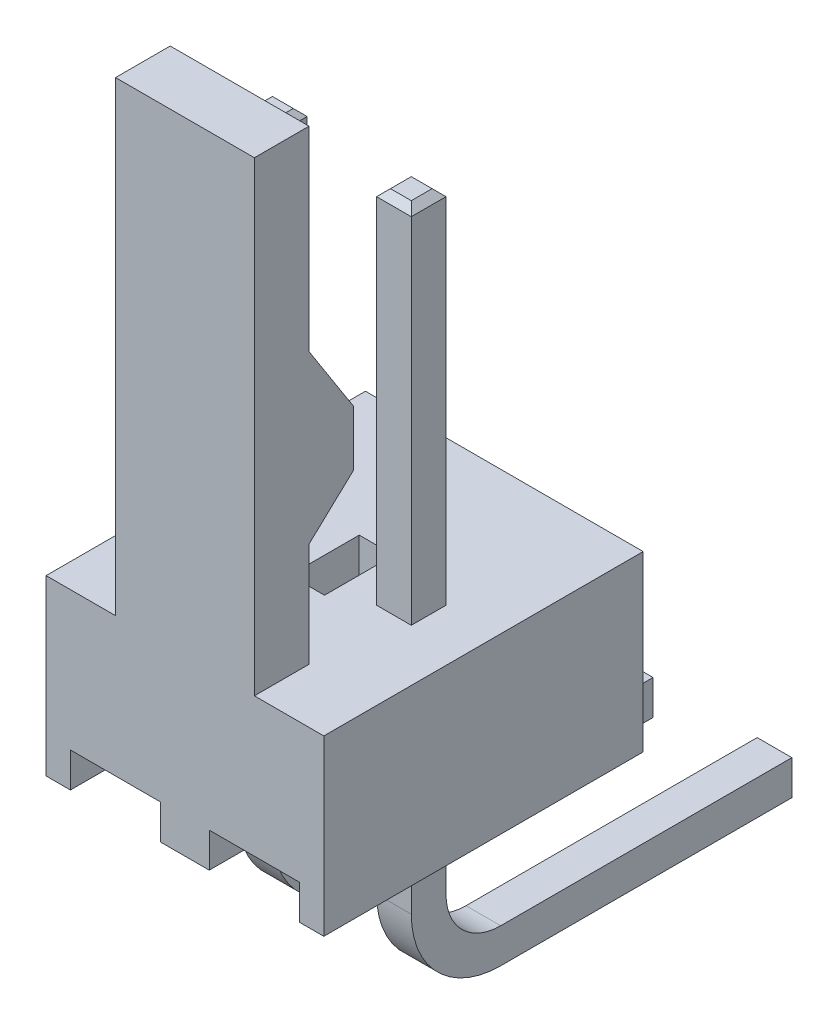
SolidWorks part; units mm, degrees
ref_plane "Płaszczyzna przednia" through (0, 0, 0) normal (0, 0, 1) x (1, 0, 0)
ref_plane "Płaszczyzna górna" through (0, 0, 0) normal (0, 1, 0) x (1, 0, 0)
ref_plane "Płaszczyzna prawa" through (0, 0, 0) normal (1, 0, 0) x (0, 0, -1)
ref_plane "Plane15" through (1.5875, 0, 0) normal (1, 0, 0) x (0, 0, -1)
sketch "Sketch68" plane through (1.5875, 0, 0) normal (1, 0, 0) x (0, 0, -1)
  line L0 (3.8, -0.3175) -> (3.8, 3.355)
  line L1 (3.8, 3.355) -> (-3.2893, 3.355)
  line L2 (-3.2893, 3.355) -> (-3.2893, -0.3175)
  line L3 (-3.2893, -0.3175) -> (3.8, -0.3175)
extrude "Boss-Extrude17" add sketch "Sketch68" against normal blind 0.635 separate body
sketch "Sketch69" plane through (0.9525, 0, 0) normal (-1, 0, 0) x (0, 0, 1)
  line L0 (-3.8, 0.3175) -> (2.6543, 0.3175)
  line L1 (2.6543, 0.3175) -> (2.6543, 3.355)
  line L2 (2.6543, 3.355) -> (-3.8, 3.355)
  line L3 (-3.8, 3.355) -> (-3.8, 0.3175)
extrude "Cut-Extrude12" cut sketch "Sketch69" against normal through all
chamfer "Chamfer15" distance 0.127 angle 45 4 edges at (0.9525, 0, -3.8) (1.27, -0.3175, -3.8) (1.27, 0.3175, -3.8) (1.5875, 0, -3.8)
fillet "Fillet17" radius 1 1 edges at (1.27, 0.3175, 2.6543)
fillet "Fillet18" radius 1.635 1 edges at (1.27, -0.3175, 3.2893)
ref_plane "Plane16" through (-0.9525, 0, 0) normal (1, 0, 0) x (0, 0, -1)
sketch "Sketch74" plane through (-0.9525, 0, 0) normal (1, 0, 0) x (0, 0, -1)
  line L0 (3.8, -0.3175) -> (3.8, 3.355)
  line L1 (3.8, 3.355) -> (-3.2893, 3.355)
  line L2 (-3.2893, 3.355) -> (-3.2893, -0.3175)
  line L3 (-3.2893, -0.3175) -> (3.8, -0.3175)
extrude "Boss-Extrude18" add sketch "Sketch74" against normal blind 0.635 separate body
sketch "Sketch75" plane through (-1.5875, 0, 0) normal (-1, 0, 0) x (0, 0, 1)
  line L0 (-3.8, 0.3175) -> (2.6543, 0.3175)
  line L1 (2.6543, 0.3175) -> (2.6543, 3.355)
  line L2 (2.6543, 3.355) -> (-3.8, 3.355)
  line L3 (-3.8, 3.355) -> (-3.8, 0.3175)
extrude "Cut-Extrude13" cut sketch "Sketch75" against normal through all
chamfer "Chamfer16" distance 0.127 angle 45 4 edges at (-1.5875, 0, -3.8) (-1.27, -0.3175, -3.8) (-1.27, 0.3175, -3.8) (-0.9525, 0, -3.8)
fillet "Fillet19" radius 1 1 edges at (-1.27, 0.3175, 2.6543)
fillet "Fillet20" radius 1.635 1 edges at (-1.27, -0.3175, 3.2893)
ref_plane "Plane17" through (0, 0, 2.6543) normal (0, 0, -1) x (-1, 0, 0)
sketch "Sketch81" plane through (0, 0, 2.6543) normal (0, 0, -1) x (-1, 0, 0)
  line L0 (-0.9525, 5.895) -> (-0.9525, 12.368)
  line L1 (-0.9525, 12.368) -> (-0.9525, 12.495)
  line L2 (-0.9525, 12.495) -> (-1.5875, 12.495)
  line L3 (-1.5875, 12.495) -> (-1.5875, 12.368)
  line L4 (-1.5875, 12.368) -> (-1.5875, 5.895)
  line L5 (-1.5875, 5.895) -> (-0.9525, 5.895)
extrude "Boss-Extrude19" add sketch "Sketch81" against normal blind 0.635 separate body
chamfer "Chamfer17" distance 0.127 angle 45 4 edges at (1.27, 12.495, 3.2893) (0.9525, 12.495, 2.9718) (1.5875, 12.495, 2.9718) (1.27, 12.495, 2.6543)
sketch "Sketch88" plane through (0, 0, 2.6543) normal (0, 0, -1) x (-1, 0, 0)
  line L0 (1.5875, 5.895) -> (1.5875, 12.368)
  line L1 (1.5875, 12.368) -> (1.5875, 12.495)
  line L2 (1.5875, 12.495) -> (0.9525, 12.495)
  line L3 (0.9525, 12.495) -> (0.9525, 12.368)
  line L4 (0.9525, 12.368) -> (0.9525, 5.895)
  line L5 (0.9525, 5.895) -> (1.5875, 5.895)
extrude "Boss-Extrude20" add sketch "Sketch88" against normal blind 0.635 separate body
chamfer "Chamfer18" distance 0.127 angle 45 4 edges at (-1.27, 12.495, 3.2893) (-1.5875, 12.495, 2.9718) (-0.9525, 12.495, 2.9718) (-1.27, 12.495, 2.6543)
ref_plane "Plane18" through (0, 2.72, 0) normal (0, -1, 0) x (-1, 0, 0)
sketch "Sketch95" plane through (0, 2.72, 0) normal (0, -1, 0) x (-1, 0, 0)
  line L0 (-2.54, -5.842) -> (1.27, -5.842)
  line L1 (1.27, -5.842) -> (1.27, 0)
  line L2 (1.27, 0) -> (-2.54, 0)
  line L3 (-2.54, 0) -> (-2.54, -5.842)
extrude "Boss-Extrude21" add sketch "Sketch95" against normal blind 3.175 separate body
ref_plane "Plane19" through (-1.27, 0, 0) normal (-1, 0, 0) x (0, 0, 1)
sketch "Sketch103" plane through (-1.27, 0, 0) normal (-1, 0, 0) x (0, 0, 1)
  line L0 (4.842, 7.8) -> (4.842, 5.895)
  line L1 (4.842, 5.895) -> (5.842, 5.895)
  line L2 (5.842, 5.895) -> (5.842, 14.42)
  line L3 (5.842, 14.42) -> (4.842, 14.42)
  line L4 (4.842, 14.42) -> (4.842, 10.848)
  line L5 (4.842, 10.848) -> (3.6228, 8.943)
  line L6 (3.6228, 8.943) -> (4.842, 7.8)
extrude "Boss-Extrude22" add sketch "Sketch103" against normal blind 2.54
sketch "Sketch104" plane through (-1.27, 0, 0) normal (-1, 0, 0) x (0, 0, 1)
  line L0 (5.842, 2.72) -> (0, 2.72)
  line L1 (0, 2.72) -> (0, 5.895)
  line L2 (0, 5.895) -> (5.842, 5.895)
  line L3 (5.842, 5.895) -> (5.842, 2.72)
extrude "Boss-Extrude23" add sketch "Sketch104" along normal blind 1.27
sketch "Sketch105" plane through (0, 0, 5.842) normal (0, 0, 1) x (1, 0, 0)
  line L0 (0.4445, 2.72) -> (2.0955, 2.72)
  line L1 (2.0955, 2.72) -> (2.0955, 3.355)
  line L2 (2.0955, 3.355) -> (0.4445, 3.355)
  line L3 (0.4445, 3.355) -> (0.4445, 2.72)
extrude "Cut-Extrude14" cut sketch "Sketch105" against normal through all
sketch "Sketch106" plane through (0, 0, 5.842) normal (0, 0, 1) x (1, 0, 0)
  line L0 (-2.0955, 2.72) -> (-0.4445, 2.72)
  line L1 (-0.4445, 2.72) -> (-0.4445, 3.355)
  line L2 (-0.4445, 3.355) -> (-2.0955, 3.355)
  line L3 (-2.0955, 3.355) -> (-2.0955, 2.72)
extrude "Cut-Extrude15" cut sketch "Sketch106" against normal through all
sketch "Sketch107" plane through (0, 5.895, 0) normal (0, 1, 0) x (-1, 0, 0)
  line L0 (-0.3175, 3.6068) -> (-0.3175, 2.3368)
  line L1 (-0.3175, 2.3368) -> (0.3175, 2.3368)
  line L2 (0.3175, 2.3368) -> (0.3175, 3.6068)
  line L3 (0.3175, 3.6068) -> (-0.3175, 3.6068)
extrude "Cut-Extrude16" cut sketch "Sketch107" against normal blind 1.27
chamfer "Chamfer19" distance 0.5571 angle 46.848 1 edges at (0, 8.943, 3.6228)
